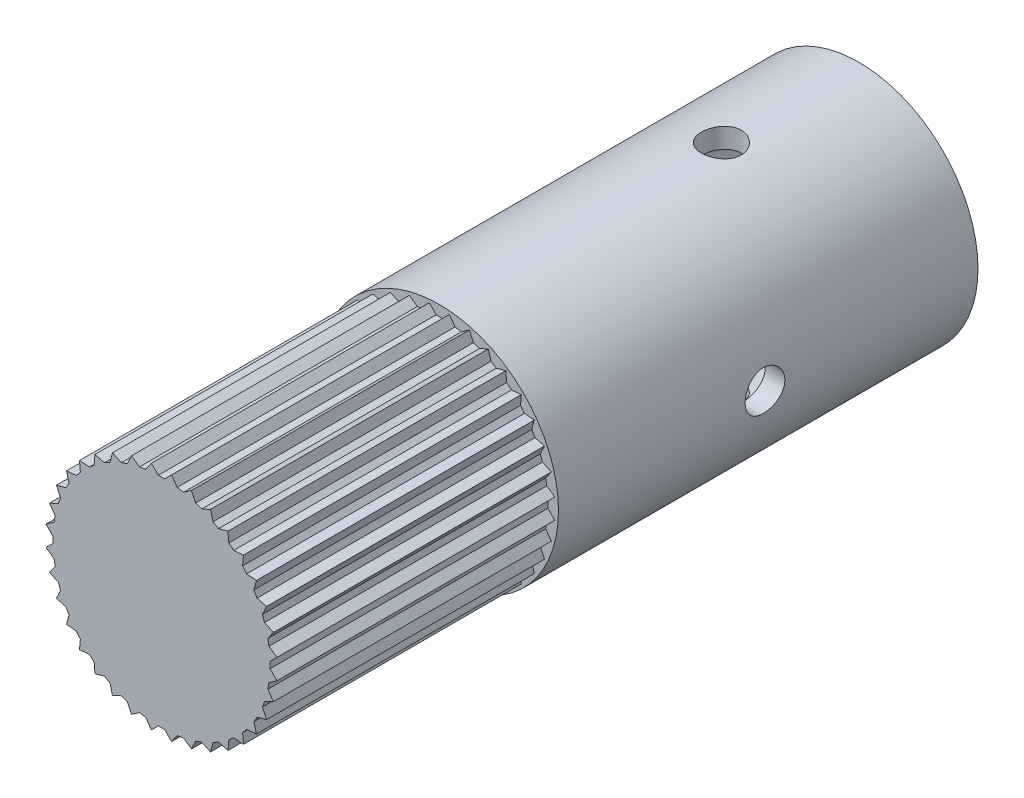
SolidWorks part; units mm, degrees
material "AISI 1015 Steel, Cold Drawn (SS)"
ref_plane "X-Y Datum" through (0, 0, 0) normal (0, 0, 1) x (1, 0, 0)
ref_plane "X-Z Datum" through (0, 0, 0) normal (0, 1, 0) x (1, 0, 0)
ref_plane "Y-Z Datum" through (0, 0, 0) normal (1, 0, 0) x (0, 0, -1)
sketch "Sketch9" plane through (0, 0, 0) normal (0, 1, 0) x (1, 0, 0)
  line L0 (16.002, 0) -> (0, 0)
  line L1 (0, 0) -> (0, -389.0916)
  line L2 (0, -389.0916) -> (-72.2493, -524.9728)
  dimension "D1" = 153.895
  dimension "D2" = 28
  dimension "D3" = 389.0916
  dimension "D5" = 16.002
sketch "Sketch5" plane through (0, 0, 0) normal (0, 1, 0) x (1, 0, 0)
  line L0 (7.9375, -77.9416) -> (7.9375, -22.1615)
  line L1 (7.9375, -22.1615) -> (9.525, -22.1615)
  line L2 (9.525, -22.1615) -> (9.525, -77.9416)
  line L3 (9.525, -77.9416) -> (7.9375, -77.9416)
  line L5 (16.002, 0) -> (0, 0) construction
  line L6 (0, 0) -> (0, -389.0916) construction
  line L7 (0, -389.0916) -> (9.525, -389.0916) construction
  line L8 (12.5602, -58.6916) -> (0, -58.6916) construction
  dimension "D1" = 1.5875
  dimension "D2" = 22.1615
  dimension "D3" = 7.9375
  dimension "D4" = 330.4
  dimension "D5" = 311.15
revolve "Revolve2" add sketch "Sketch5" angle 360 about L1
sketch "Sketch6" plane through (0, 0, 0) normal (0, 1, 0) x (1, 0, 0)
  circle A0 centre (0, -33.1635) radius 1.5875 construction
  circle A1 centre (0, -33.1635) radius 1.5875
sketch "Sketch7" plane through (0, 0, 0) normal (1, 0, 0) x (0, 0, -1)
  circle A2 centre (-39.196, 0) radius 1.5875
  circle A4 centre (-39.196, 0) radius 1.5875 construction
extrude "Cut-Extrude5" cut sketch "Sketch7" against normal through all both and the other way through all
extrude "Cut-Extrude6" cut sketch "Sketch6" against normal through all both and the other way through all
sketch "Sketch8" plane through (0, 0, 0) normal (0, 0, 1) x (1, 0, 0)
  line L0 (9.2357, -0.808) -> (8.6817, -0.254)
  line L1 (8.6817, -0.254) -> (8.6817, 0.254)
  line L2 (8.6817, 0.254) -> (9.2357, 0.808)
  line L3 (8.6817, 0) -> (0, 0) construction
  line L4 (8.9551, -2.3995) -> (8.5057, -1.7577)
  line L5 (8.5057, -1.7577) -> (8.5939, -1.2574)
  line L6 (8.5939, -1.2574) -> (9.2357, -0.808)
  line L7 (8.4024, -3.9181) -> (8.0713, -3.208)
  line L8 (8.0713, -3.208) -> (8.245, -2.7306)
  line L9 (8.245, -2.7306) -> (8.9551, -2.3995)
  line L10 (7.5944, -5.3176) -> (7.3916, -4.5608)
  line L11 (7.3916, -4.5608) -> (7.6456, -4.1209)
  line L12 (7.6456, -4.1209) -> (8.4024, -3.9181)
  line L13 (6.5556, -6.5556) -> (6.4873, -5.7751)
  line L14 (6.4873, -5.7751) -> (6.8138, -5.3859)
  line L15 (6.8138, -5.3859) -> (7.5944, -5.3176)
  line L16 (5.3176, -7.5944) -> (5.3859, -6.8138)
  line L17 (5.3859, -6.8138) -> (5.7751, -6.4873)
  line L18 (5.7751, -6.4873) -> (6.5556, -6.5556)
  line L19 (3.9181, -8.4024) -> (4.1209, -7.6456)
  line L20 (4.1209, -7.6456) -> (4.5608, -7.3916)
  line L21 (4.5608, -7.3916) -> (5.3176, -7.5944)
  line L22 (2.3995, -8.9551) -> (2.7306, -8.245)
  line L23 (2.7306, -8.245) -> (3.208, -8.0713)
  line L24 (3.208, -8.0713) -> (3.9181, -8.4024)
  line L25 (0.808, -9.2357) -> (1.2574, -8.5939)
  line L26 (1.2574, -8.5939) -> (1.7577, -8.5057)
  line L27 (1.7577, -8.5057) -> (2.3995, -8.9551)
  line L28 (-0.808, -9.2357) -> (-0.254, -8.6817)
  line L29 (-0.254, -8.6817) -> (0.254, -8.6817)
  line L30 (0.254, -8.6817) -> (0.808, -9.2357)
  line L31 (-2.3995, -8.9551) -> (-1.7577, -8.5057)
  line L32 (-1.7577, -8.5057) -> (-1.2574, -8.5939)
  line L33 (-1.2574, -8.5939) -> (-0.808, -9.2357)
  line L34 (-3.9181, -8.4024) -> (-3.208, -8.0713)
  line L35 (-3.208, -8.0713) -> (-2.7306, -8.245)
  line L36 (-2.7306, -8.245) -> (-2.3995, -8.9551)
  line L37 (-5.3176, -7.5944) -> (-4.5608, -7.3916)
  line L38 (-4.5608, -7.3916) -> (-4.1209, -7.6456)
  line L39 (-4.1209, -7.6456) -> (-3.9181, -8.4024)
  line L40 (-6.5556, -6.5556) -> (-5.7751, -6.4873)
  line L41 (-5.7751, -6.4873) -> (-5.3859, -6.8138)
  line L42 (-5.3859, -6.8138) -> (-5.3176, -7.5944)
  line L43 (-7.5944, -5.3176) -> (-6.8138, -5.3859)
  line L44 (-6.8138, -5.3859) -> (-6.4873, -5.7751)
  line L45 (-6.4873, -5.7751) -> (-6.5556, -6.5556)
  line L46 (-8.4024, -3.9181) -> (-7.6456, -4.1209)
  line L47 (-7.6456, -4.1209) -> (-7.3916, -4.5608)
  line L48 (-7.3916, -4.5608) -> (-7.5944, -5.3176)
  line L49 (-8.9551, -2.3995) -> (-8.245, -2.7306)
  line L50 (-8.245, -2.7306) -> (-8.0713, -3.208)
  line L51 (-8.0713, -3.208) -> (-8.4024, -3.9181)
  line L52 (-9.2357, -0.808) -> (-8.5939, -1.2574)
  line L53 (-8.5939, -1.2574) -> (-8.5057, -1.7577)
  line L54 (-8.5057, -1.7577) -> (-8.9551, -2.3995)
  line L55 (-9.2357, 0.808) -> (-8.6817, 0.254)
  line L56 (-8.6817, 0.254) -> (-8.6817, -0.254)
  line L57 (-8.6817, -0.254) -> (-9.2357, -0.808)
  line L58 (-8.9551, 2.3995) -> (-8.5057, 1.7577)
  line L59 (-8.5057, 1.7577) -> (-8.5939, 1.2574)
  line L60 (-8.5939, 1.2574) -> (-9.2357, 0.808)
  line L61 (-8.4024, 3.9181) -> (-8.0713, 3.208)
  line L62 (-8.0713, 3.208) -> (-8.245, 2.7306)
  line L63 (-8.245, 2.7306) -> (-8.9551, 2.3995)
  line L64 (-7.5944, 5.3176) -> (-7.3916, 4.5608)
  line L65 (-7.3916, 4.5608) -> (-7.6456, 4.1209)
  line L66 (-7.6456, 4.1209) -> (-8.4024, 3.9181)
  line L67 (-6.5556, 6.5556) -> (-6.4873, 5.7751)
  line L68 (-6.4873, 5.7751) -> (-6.8138, 5.3859)
  line L69 (-6.8138, 5.3859) -> (-7.5944, 5.3176)
  line L70 (-5.3176, 7.5944) -> (-5.3859, 6.8138)
  line L71 (-5.3859, 6.8138) -> (-5.7751, 6.4873)
  line L72 (-5.7751, 6.4873) -> (-6.5556, 6.5556)
  line L73 (-3.9181, 8.4024) -> (-4.1209, 7.6456)
  line L74 (-4.1209, 7.6456) -> (-4.5608, 7.3916)
  line L75 (-4.5608, 7.3916) -> (-5.3176, 7.5944)
  line L76 (-2.3995, 8.9551) -> (-2.7306, 8.245)
  line L77 (-2.7306, 8.245) -> (-3.208, 8.0713)
  line L78 (-3.208, 8.0713) -> (-3.9181, 8.4024)
  line L79 (-0.808, 9.2357) -> (-1.2574, 8.5939)
  line L80 (-1.2574, 8.5939) -> (-1.7577, 8.5057)
  line L81 (-1.7577, 8.5057) -> (-2.3995, 8.9551)
  line L82 (0.808, 9.2357) -> (0.254, 8.6817)
  line L83 (0.254, 8.6817) -> (-0.254, 8.6817)
  line L84 (-0.254, 8.6817) -> (-0.808, 9.2357)
  line L85 (2.3995, 8.9551) -> (1.7577, 8.5057)
  line L86 (1.7577, 8.5057) -> (1.2574, 8.5939)
  line L87 (1.2574, 8.5939) -> (0.808, 9.2357)
  line L88 (3.9181, 8.4024) -> (3.208, 8.0713)
  line L89 (3.208, 8.0713) -> (2.7306, 8.245)
  line L90 (2.7306, 8.245) -> (2.3995, 8.9551)
  line L91 (5.3176, 7.5944) -> (4.5608, 7.3916)
  line L92 (4.5608, 7.3916) -> (4.1209, 7.6456)
  line L93 (4.1209, 7.6456) -> (3.9181, 8.4024)
  line L94 (6.5556, 6.5556) -> (5.7751, 6.4873)
  line L95 (5.7751, 6.4873) -> (5.3859, 6.8138)
  line L96 (5.3859, 6.8138) -> (5.3176, 7.5944)
  line L97 (7.5944, 5.3176) -> (6.8138, 5.3859)
  line L98 (6.8138, 5.3859) -> (6.4873, 5.7751)
  line L99 (6.4873, 5.7751) -> (6.5556, 6.5556)
  line L100 (8.4024, 3.9181) -> (7.6456, 4.1209)
  line L101 (7.6456, 4.1209) -> (7.3916, 4.5608)
  line L102 (7.3916, 4.5608) -> (7.5944, 5.3176)
  line L103 (8.9551, 2.3995) -> (8.245, 2.7306)
  line L104 (8.245, 2.7306) -> (8.0713, 3.208)
  line L105 (8.0713, 3.208) -> (8.4024, 3.9181)
  line L106 (9.2357, 0.808) -> (8.5939, 1.2574)
  line L107 (8.5939, 1.2574) -> (8.5057, 1.7577)
  line L108 (8.5057, 1.7577) -> (8.9551, 2.3995)
  circle A0 centre (0, 0) radius 12.7
  circle A1 centre (0, 0) radius 9.271 construction
  circle A2 centre (0, 0) radius 8.6854 construction
  point P153 (0, 0)
  dimension "D1" = 25.4
  dimension "D4" = 18.542
  dimension "D6" = 17.3708
  dimension "D2" = 0.508
  dimension "D3" = 135
  dimension "D5" = 36
extrude "Cut-Extrude7" cut sketch "Sketch8" against normal blind 22.225 from surface at 77.9416 starting at face at (-9.525, 0, 77.9416)
ref_plane "Plane1" through (0, 0, 47.5615) normal (0, 0, -1) x (-1, 0, 0)
sketch "Sketch10" plane through (0, 0, 47.5615) normal (0, 0, -1) x (-1, 0, 0)
  circle A0 centre (0, 0) radius 7.9375
  dimension "D1" = 15.875
extrude "Boss-Extrude1" add sketch "Sketch10" against normal up to surface (30.3801 mm away) up to face at (-7.9375, 0, 77.9416)
sketch "Sketch11" plane through (0, 0, 22.1615) normal (0, 0, -1) x (-1, 0, 0)
  line L0 (0, 9.525) -> (13.3548, 9.525) construction
  line L1 (0, 9.525) -> (0, 15.4312) construction
  line L2 (-9.525, 0) -> (-9.525, 9.1744) construction
  line L3 (-9.525, 0) -> (-16.674, 0) construction
  circle A0 centre (0, 0) radius 9.525 construction
  point P0 (0, 9.525)
  point P1 (-9.525, 0)
